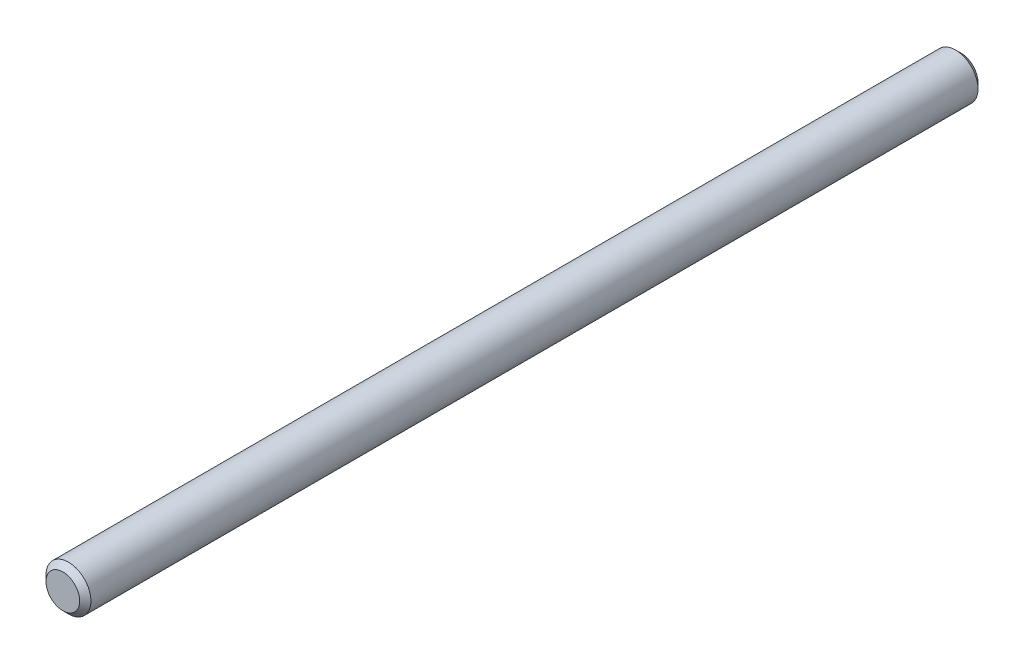
SolidWorks part; units mm, degrees
ref_plane "Plano frontal" through (0, 0, 0) normal (0, 0, 1) x (1, 0, 0)
ref_plane "Plano superior" through (0, 0, 0) normal (0, 1, 0) x (1, 0, 0)
ref_plane "Plano direito" through (0, 0, 0) normal (1, 0, 0) x (0, 0, -1)
sketch "Esboço1" plane through (0, 0, 0) normal (0, 0, 1) x (1, 0, 0)
  circle A0 centre (0, 0) radius 4
  dimension "D1" = 8
extrude "Ressalto-extrusão1" add sketch "Esboço1" along normal blind 160
chamfer "Chanfro1" distance 1 angle 45 2 edges at (4, 0, 160) (4, 0, 0)
